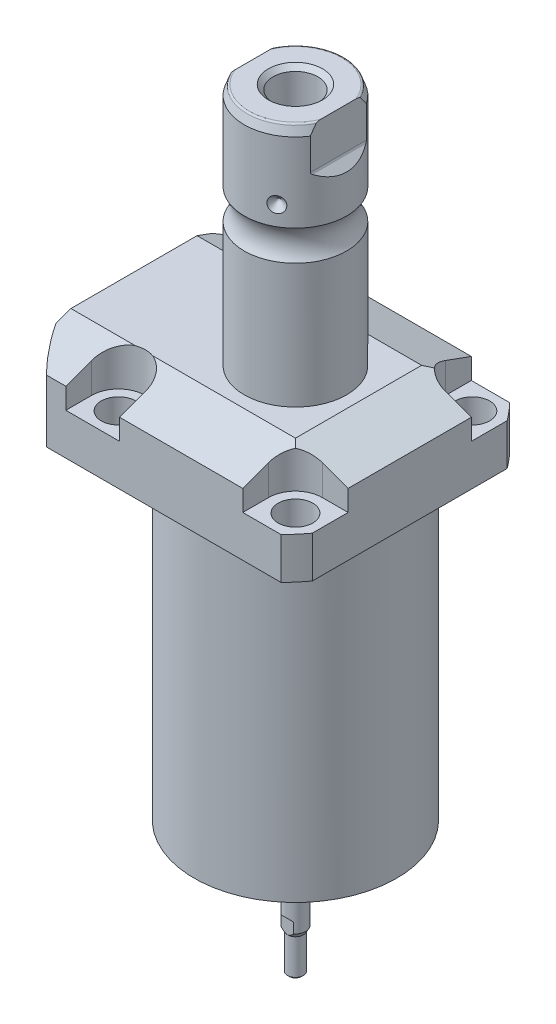
SolidWorks part; units mm, degrees
material "Alloy Steel"
ref_plane "Front Plane" through (0, 0, 0) normal (0, 0, 1) x (1, 0, 0)
ref_plane "Top Plane" through (0, 0, 0) normal (0, 1, 0) x (1, 0, 0)
ref_plane "Right Plane" through (0, 0, 0) normal (1, 0, 0) x (0, 0, -1)
sketch "Sketch1" plane through (0, 0, 0) normal (0, -1, 0) x (0, 0, 1)
  line L0 (-35.433, 50.063) -> (35.433, 50.063)
  line L1 (35.433, 50.063) -> (35.433, -35.433)
  line L2 (35.433, -35.433) -> (-35.433, -35.433)
  line L3 (-35.433, -35.433) -> (-35.433, 50.063)
  line L4 (0, 0) -> (0, -60.6467) construction
  dimension "D1" = 35.433
  dimension "D2" = 85.496
  dimension "D3" = 70.866
extrude "Extrude1" add sketch "Sketch1" against normal blind 122.047
sketch "Sketch2" plane through (0, 0, 0) normal (0, -1, 0) x (1, 0, 0)
  circle A0 centre (-5.4102, 0) radius 50.8
  dimension "D1" = 101.6
  dimension "D2" = 5.4102
extrude "Cut-Extrude1" cut sketch "Sketch2" against normal through all flip side to cut
sketch "Sketch3" plane through (0, 0, 0) normal (1, 0, 0) x (0, 0, -1)
  line L0 (31.3945, 0) -> (31.3945, 96.9518)
  line L1 (31.3945, 96.9518) -> (76.5937, 96.9518)
  line L2 (76.5937, 96.9518) -> (76.5937, 0)
  line L3 (76.5937, 0) -> (31.3945, 0)
  line L4 (0, -93.345) -> (0, 4.445) construction
  line L5 (24.2233, 0) -> (-24.2233, 0) construction
  dimension "D1" = 62.789
  dimension "D2" = 153.1874
  dimension "D3" = 96.9518
revolve "Cut-Revolve1" cut sketch "Sketch3" angle 360 about L4
fillet "Fillet1" radius 0.381 1 edges at (0, 96.9518, -31.3945)
sketch "Sketch4" plane through (0, 122.047, 0) normal (0, 1, 0) x (-1, 0, 0)
  line L0 (-35.433, -30.2072) -> (-35.433, 30.2072) construction
  line L1 (41.8127, 35.433) -> (-30.9923, 35.433) construction
  line L2 (-19.1008, -35.433) -> (-19.1008, -27.432)
  line L3 (-35.433, -35.433) -> (-19.1008, -35.433)
  line L4 (-35.433, -19.1008) -> (-35.433, -35.433)
  line L5 (-27.432, -19.1008) -> (-35.433, -19.1008)
  line L6 (35.7632, -35.433) -> (19.1008, -35.433)
  line L7 (19.1008, 35.433) -> (19.1008, 27.432)
  line L8 (35.7632, 35.433) -> (35.7632, 27.432)
  line L9 (35.7632, 35.433) -> (19.1008, 35.433)
  line L10 (-27.432, 19.1008) -> (-35.433, 19.1008)
  line L11 (-35.433, 19.1008) -> (-35.433, 35.433)
  line L12 (-35.433, 35.433) -> (-19.1008, 35.433)
  line L13 (-19.1008, 35.433) -> (-19.1008, 27.432)
  line L14 (-48.9217, 0) -> (49.4551, 0) construction
  line L15 (35.7632, -35.433) -> (35.7632, -27.432)
  line L16 (19.1008, -35.433) -> (19.1008, -27.432)
  arc A0 (19.1008, -27.432) -> (35.7632, -27.432) centre (27.432, -27.432) cw
  arc A1 (-27.432, -19.1008) -> (-19.1008, -27.432) centre (-27.432, -27.432) cw
  arc A2 (-27.432, 19.1008) -> (-19.1008, 27.432) centre (-27.432, 27.432) ccw
  arc A3 (19.1008, 27.432) -> (35.7632, 27.432) centre (27.432, 27.432) ccw
  dimension "D2" = 8.3312
  dimension "D1" = 27.432
  dimension "D3" = 27.432
  dimension "D4" = 54.864
extrude "Cut-Extrude2" cut sketch "Sketch4" against normal blind 12.243
sketch "Sketch5" plane through (0, 0, 0) normal (1, 0, 0) x (0, 0, -1)
  line L0 (-19.558, 122.047) -> (-35.433, 116.269)
  line L1 (0, 0) -> (0, 154.1081) construction
  line L2 (-19.558, 122.047) -> (-35.433, 122.047)
  line L3 (-35.433, 122.047) -> (-35.433, 116.269)
  dimension "D1" = 15.875
  dimension "D2" = 20
extrude "Cut-Extrude9" cut sketch "Sketch5" against normal through all and the other way through all
mirror "Mirror1" about plane through (0, 0, 0) normal (0, 0, 1) of "Cut-Extrude9"
sketch "Sketch9" plane through (0, 0, 0) normal (0, 0, 1) x (1, 0, 0)
  line L0 (19.558, 122.047) -> (35.433, 116.269)
  line L1 (35.433, 116.269) -> (35.433, 122.047)
  line L2 (35.433, 122.047) -> (19.558, 122.047)
  dimension "D1" = 15.875
  dimension "D2" = 20
extrude "Cut-Extrude7" cut sketch "Sketch9" against normal through all and the other way through all
ref_plane "Plane14" through (-35.0774, 0, 0) normal (1, 0, 0) x (0, 0, -1)
sketch "Sketch20" plane through (-35.0774, 88.9, -18.1102) normal (1, 0, 0) x (0, 1, 0)
  line L0 (-88.9, 18.1102) -> (39.8401, 18.1102) construction
  line L1 (-7.2797, 32.639) -> (36.9042, 32.639) construction
  line L2 (8.0518, 38.3413) -> (9.4996, 38.3413)
  line L3 (8.0518, -6.1131) -> (8.0518, 42.3335) construction
  line L4 (9.4996, 38.3413) -> (9.4996, 35.8902)
  line L5 (9.4996, 35.8902) -> (10.5156, 35.8902)
  line L6 (10.5156, 35.8902) -> (10.5156, 33.8836)
  line L7 (10.5156, 33.8836) -> (21.4884, 33.8836)
  line L8 (21.4884, 33.8836) -> (21.4884, 32.639)
  line L9 (21.4884, 32.639) -> (8.0518, 32.639)
  line L10 (8.0518, 38.3413) -> (8.0518, 32.639)
  dimension "D1" = 14.5288
  dimension "D2" = 11.4046
  dimension "D3" = 1.4478
  dimension "D4" = 6.5024
  dimension "D5" = 1.016
  dimension "D6" = 2.4892
  dimension "D7" = 10.9728
revolve "Cut-Revolve4" cut sketch "Sketch20" angle 360 about L1
mirror "Mirror10" about plane through (0, 0, 0) normal (0, 0, 1) of "Cut-Revolve4"
sketch "Sketch10" plane through (-35.0774, 88.9, -18.1102) normal (1, 0, 0) x (0, 1, 0)
  line L0 (-1.0325, 3.5814) -> (1.5659, 3.5814) construction
  line L1 (21.4884, 4.826) -> (10.5156, 4.826) construction
  line L2 (10.5156, 2.3368) -> (21.4884, 2.3368) construction
  line L4 (8.0518, -12.097) -> (8.0518, 48.3174) construction
  circle A0 centre (8.3185, 8.1026) radius 1.1811
  dimension "D1" = 2.3622
  dimension "D2" = 0.2667
  dimension "D3" = 9.0424
revolve "Revolve4" add sketch "Sketch10" angle 360 about L0
mirror "Mirror12" about plane through (0, 0, 0) normal (0, 0, 1) of bodies 135
sketch "Sketch15" plane through (0, 0, 0) normal (1, 0, 0) x (0, 0, -1)
  line L0 (0, 122.047) -> (15.875, 122.047)
  line L1 (15.875, 122.047) -> (15.875, 160.6719)
  line L2 (15.875, 170.0861) -> (15.875, 194.564)
  line L3 (14.8118, 197.485) -> (0, 197.485)
  line L4 (0, 197.485) -> (0, 122.047)
  line L5 (0, 250.2908) -> (0, 28.9095) construction
  line L6 (19.558, 122.047) -> (-19.558, 122.047) construction
  line L7 (14.8118, 197.485) -> (15.875, 194.564)
  line L9 (24.2233, 96.9518) -> (35.433, 96.9518) construction
  arc A0 (15.875, 170.0861) -> (15.875, 160.6719) centre (22.2504, 165.379) ccw
  dimension "D2" = 20
  dimension "D4" = 7.9248
  dimension "D6" = 28.6512
  dimension "D1" = 100.5332
  dimension "D3" = 31.75
  dimension "D5" = 32.106
  dimension "D7" = 2.921
revolve "Revolve3" add sketch "Sketch15" angle 360 about L5
hole_wizard "Hole1" positions "Sketch18" profile "Sketch17" legacy end condition up to next
sketch "Sketch18" plane through (0, 109.804, 0) normal (0, 1, 0) x (-1, 0, 0)
  arc A0 (35.7632, -27.432) -> (19.1008, -27.432) centre (27.432, -27.432) ccw construction
  arc A1 (19.1008, 27.432) -> (35.7632, 27.432) centre (27.432, 27.432) ccw construction
  arc A2 (-27.432, 19.1008) -> (-19.1008, 27.432) centre (-27.432, 27.432) ccw construction
  arc A3 (-19.1008, -27.432) -> (-27.432, -19.1008) centre (-27.432, -27.432) ccw construction
  point P0 (-27.432, -27.432)
  point P1 (-27.432, 27.432)
  point P3 (27.432, 27.432)
  point P5 (27.432, -27.432)
sketch "Sketch17" plane through (27.432, 109.804, -27.432) normal (1, 0, 0) x (0, 0, 1)
  line L0 (0, 0) -> (0, 12.8522)
  line L1 (0, 12.8522) -> (5.3594, 12.8522)
  line L2 (5.3594, 12.8522) -> (5.3594, 0)
  line L3 (5.3594, 0) -> (0, 0)
  line L4 (0, 110) -> (0, -10) construction
  dimension "Diameter" = 10.7188
  dimension "Depth" = 12.8522
chamfer "Chamfer1" distance 0.635 angle 45 2 edges at (-35.0774, 99.4156, 13.2842) (-35.0774, 99.4156, -13.2842)
ref_plane "Plane15" through (0, 109.4486, 0) normal (0, -1, 0) x (1, 0, 0)
sketch "Sketch21" plane through (0, 109.4486, 0) normal (0, -1, 0) x (1, 0, 0)
  line L0 (-57.5495, -12.9794) -> (-2.9353, -12.9794) construction
  line L1 (-50.063, -1.9304) -> (-49.809, -1.9304)
  line L2 (-49.809, -1.9304) -> (-49.809, -6.7564)
  line L3 (-49.809, -6.7564) -> (-47.2563, -7.4404)
  line L4 (-46.6957, -8.001) -> (-30.759, -8.001)
  line L5 (-30.759, -8.001) -> (-30.759, -12.9794)
  line L6 (-30.759, -12.9794) -> (-50.063, -12.9794)
  line L7 (-50.063, 24.2233) -> (-50.063, -24.2233) construction
  line L8 (-50.063, -12.9794) -> (-50.063, -1.9304)
  line L9 (-47.2563, -7.4404) -> (-46.6957, -8.001)
  dimension "D1" = 12.9794
  dimension "D2" = 0.254
  dimension "D3" = 22.098
  dimension "D4" = 45
  dimension "D5" = 2.5527
  dimension "D6" = 9.9568
  dimension "D7" = 19.05
  dimension "D8" = 15
  dimension "D9" = 12.446
revolve "Cut-Revolve5" cut sketch "Sketch21" angle 360 about L0
mirror "Mirror13" about plane through (0, 0, 0) normal (0, 0, 1) of "Cut-Revolve5"
fillet "Fillet2" radius 0.635 1 edges at (0, 197.485, 14.8118)
sketch "Sketch26" plane through (0, 0, 0) normal (0, 0, 1) x (1, 0, 0)
  line L0 (-39.772, 176.047) -> (35.3173, 176.047) construction
  line L1 (-15.875, 178.46) -> (-13.462, 176.047)
  line L2 (-15.875, 194.564) -> (-15.875, 170.0861) construction
  line L3 (-13.462, 176.047) -> (-15.875, 176.047)
  line L4 (-15.875, 176.047) -> (-15.875, 178.46)
  arc A0 (-15.875, 160.6719) -> (-15.875, 170.0861) centre (-22.2504, 165.379) ccw construction
  dimension "D1" = 45
  dimension "D2" = 4.826
  dimension "D3" = 10.668
revolve "Cut-Revolve7" cut sketch "Sketch26" angle 360 about L0
pattern_circular "CirPattern1" count 3 over 360 about axis through (0, 250.2908, 0) along (0, 1, 0) of "Cut-Revolve7"
hole_wizard "Hole2" positions "Sketch28" profile "Sketch27" legacy
sketch "Sketch28" plane through (0, 197.485, 0) normal (0, 1, 0) x (-1, 0, 0)
  circle A0 centre (0, 0) radius 15.875 construction
  point P0 (0, 0)
sketch "Sketch27" plane through (0, 197.485, 0) normal (1, 0, 0) x (0, 0, 1)
  line L0 (0, 0) -> (0, 28.8121)
  line L1 (0, 28.8121) -> (6.9469, 24.638)
  line L2 (6.9469, 24.638) -> (6.9469, 0)
  line L4 (6.9469, 0) -> (0, 0)
  line L6 (0, 28.8121) -> (-6.9469, 24.638) construction
  line L7 (0, -4.2442) -> (0, 117.3081) construction
  dimension "Diameter" = 13.8938
  dimension "Depth" = 24.638
  dimension "Drill Angle" = 118
sketch "Sketch29" plane through (0, 0, 0) normal (0, 0, 1) x (1, 0, 0)
  line L0 (0, 0) -> (0, 192.0172) construction
  line L1 (13.284, 197.485) -> (13.284, 184.785)
  line L2 (14.3672, 197.485) -> (-14.3672, 197.485) construction
  line L3 (13.5072, 184.2462) -> (16.332, 181.4214)
  line L5 (16.332, 181.4214) -> (16.332, 197.485)
  line L6 (16.332, 197.485) -> (13.284, 197.485)
  line L7 (-16.332, 197.485) -> (-13.284, 197.485)
  line L8 (-16.332, 181.4214) -> (-16.332, 197.485)
  line L9 (-13.5072, 184.2462) -> (-16.332, 181.4214)
  line L10 (-13.284, 197.485) -> (-13.284, 184.785)
  arc A0 (13.284, 184.785) -> (13.5072, 184.2462) centre (14.046, 184.785) ccw
  arc A1 (-13.284, 184.785) -> (-13.5072, 184.2462) centre (-14.046, 184.785) cw
  dimension "D2" = 0.762
  dimension "D1" = 45
  dimension "D3" = 26.568
  dimension "D4" = 12.7
  dimension "D5" = 3.048
extrude "Cut-Extrude10" cut sketch "Sketch29" against normal through all and the other way through all
chamfer "Chamfer2" distance 1.4351 angle 45 1 edges at (0, 197.485, 6.9469)
sketch "Sketch30" plane through (0, 0, 0) normal (0, -1, 0) x (1, 0, 0)
  line L0 (0, 0) -> (18.7689, -5.0291) construction
  line L2 (47.0228, 0) -> (-47.0228, 0) construction
  line L3 (0, 0) -> (-9.7155, -16.8277) construction
  line L4 (0, 0) -> (-13.7398, -13.7398) construction
  line L5 (0, 0) -> (-9.7155, 16.8277) construction
  line L7 (0, 0) -> (-5.0291, 18.7689) construction
  circle A0 centre (0, 0) radius 19.431 construction
  circle A1 centre (19.431, 0) radius 1.27
  circle A2 centre (18.7689, -5.0291) radius 1.27
  circle A3 centre (-9.7155, -16.8277) radius 1.27
  circle A4 centre (-13.7398, -13.7398) radius 1.27
  circle A5 centre (-9.7155, 16.8277) radius 1.27
  circle A6 centre (-5.0291, 18.7689) radius 1.27
  dimension "D1" = 38.862
  dimension "D7" = 2.54
  dimension "D8" = 2.54
  dimension "D9" = 2.54
  dimension "D10" = 2.54
  dimension "D11" = 2.54
  dimension "D12" = 2.54
  dimension "D2" = 15
  dimension "D3" = 120
  dimension "D4" = 15
  dimension "D5" = 120
  dimension "D6" = 15
extrude "Cut-Extrude11" cut sketch "Sketch30" against normal blind 7.62
sketch "Sketch31" plane through (0, 0, 0) normal (1, 0, 0) x (0, 0, -1)
  line L0 (0, 61.6176) -> (0, -19.4362) construction
  line L2 (14.351, 0) -> (14.351, 1.3208)
  line L3 (-31.3945, 0) -> (31.3945, 0) construction
  line L4 (14.351, 1.3208) -> (11.6459, 1.3208)
  line L5 (11.6459, 1.3208) -> (11.6459, 0)
  line L6 (11.6459, 0) -> (14.351, 0)
  dimension "D1" = 1.3208
  dimension "D2" = 28.702
  dimension "D3" = 23.2918
revolve "Cut-Revolve8" cut sketch "Sketch31" angle 360 about L0
sketch "Sketch32" plane through (0, 0, 0) normal (1, 0, 0) x (0, 0, -1)
  line L0 (0, 46.6429) -> (0, -27.2479) construction
  line L2 (3.175, 0) -> (3.175, -28.3914)
  line L3 (-31.3945, 0) -> (31.3945, 0) construction
  line L4 (3.175, -28.3914) -> (2.4384, -29.6672)
  line L5 (2.4384, -29.6672) -> (2.4384, -40.5892)
  line L6 (2.4384, -40.5892) -> (1.9304, -41.0972)
  line L7 (1.9304, -41.0972) -> (0, -41.0972)
  line L8 (0, -41.0972) -> (0, 0)
  line L9 (0, 0) -> (3.175, 0)
  line L10 (-5.4728, 197.485) -> (-14.3672, 197.485) construction
  dimension "D1" = 6.35
  dimension "D2" = 4.8768
  dimension "D3" = 30
  dimension "D4" = 11.43
  dimension "D5" = 45
  dimension "D6" = 0.508
  dimension "D7" = 238.5822
revolve "Revolve5" add sketch "Sketch32" angle 360 about L0
sketch "Sketch33" plane through (0, 0, 0) normal (1, 0, 0) x (0, 0, -1)
  line L0 (2.5019, -29.5572) -> (2.5019, -25.2222)
  line L4 (2.4384, -29.6672) -> (3.175, -28.3914) construction
  line L7 (2.5019, -25.2222) -> (3.2639, -24.4602)
  line L12 (3.2639, -24.4602) -> (3.2639, -29.5572)
  line L13 (2.5019, -29.5572) -> (3.2639, -29.5572)
  line L14 (0, 47.0228) -> (0, -47.0228) construction
  line L15 (-1.9304, -41.0972) -> (1.9304, -41.0972) construction
  dimension "D1" = 2.5019
  dimension "D2" = 45
  dimension "D3" = 0.762
  dimension "D4" = 15.875
extrude "Cut-Extrude12" cut sketch "Sketch33" against normal mid plane 6.35
mirror "Mirror14" about plane through (0, 0, 0) normal (0, 0, 1) of "Cut-Extrude12"
